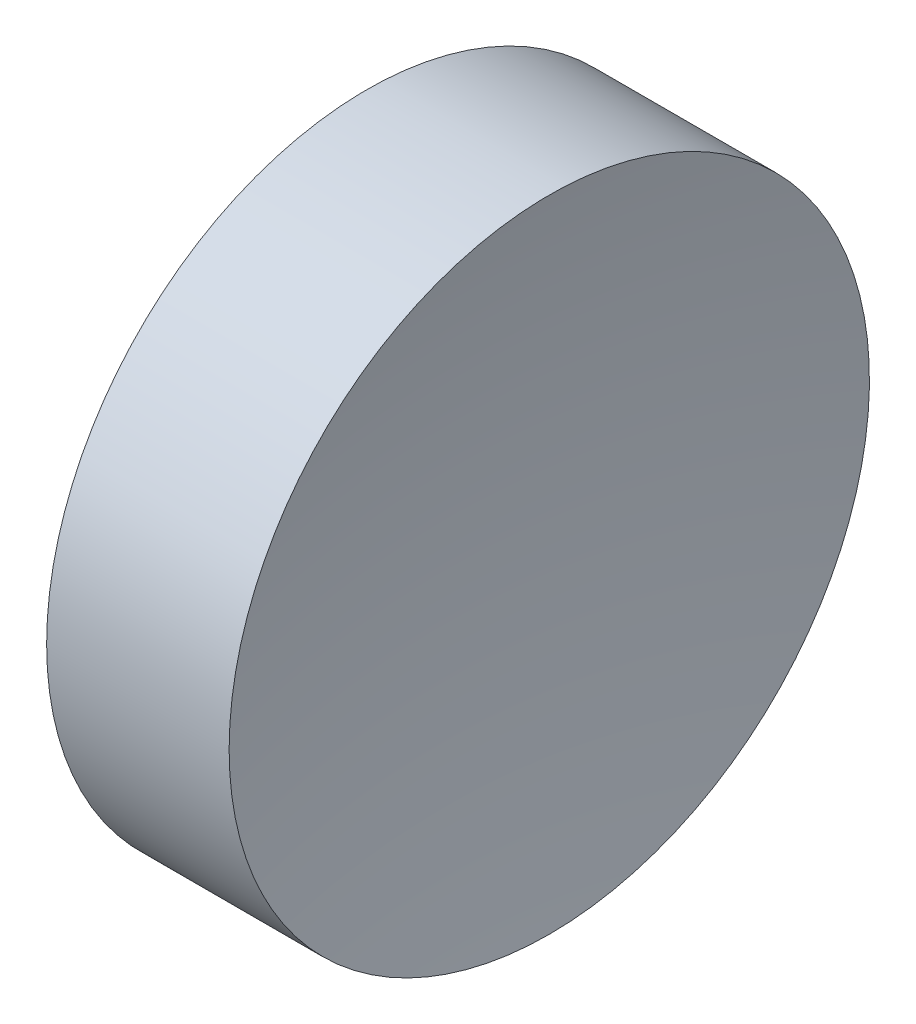
SolidWorks part; units mm, degrees
ref_plane "前视基准面" through (0, 0, 0) normal (0, 0, 1) x (1, 0, 0)
ref_plane "上视基准面" through (0, 0, 0) normal (0, 1, 0) x (1, 0, 0)
ref_plane "右视基准面" through (0, 0, 0) normal (1, 0, 0) x (0, 0, -1)
sketch "草图1" plane through (0, 0, 0) normal (0, 0, 1) x (1, 0, 0)
  line L0 (108.9851, 69.378) -> (132.7763, 69.378) construction
  line L1 (115.0927, 69.378) -> (115.0927, 81.878)
  line L2 (115.0927, 81.878) -> (122.2178, 81.878)
  line L3 (121.0927, 69.378) -> (115.0927, 69.378)
  arc A0 (122.2178, 81.878) -> (121.0927, 69.378) centre (191.0927, 69.378) ccw
revolve "旋转1" add sketch "草图1" angle 360 about L0
